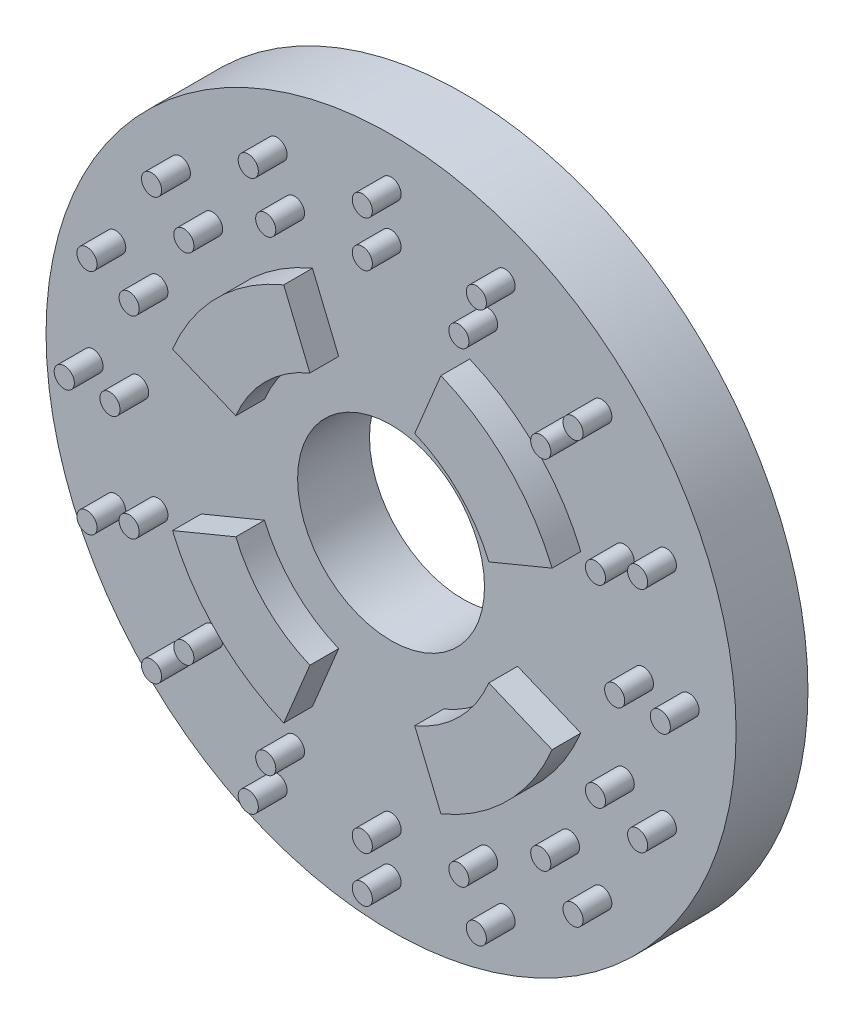
SolidWorks part; units mm, degrees
ref_plane "Front" through (0, 0, 0) normal (0, 0, 1) x (1, 0, 0)
ref_plane "Top" through (0, 0, 0) normal (0, 1, 0) x (1, 0, 0)
ref_plane "Right" through (0, 0, 0) normal (1, 0, 0) x (0, 0, -1)
sketch "Sketch1" plane through (0, 0, 0) normal (0, 0, 1) x (1, 0, 0)
  circle A0 centre (0, 0) radius 24
extrude "Extrude1" add sketch "Sketch1" along normal blind 5
sketch "Sketch4" plane through (0, 0, 5) normal (0, 0, 1) x (1, 0, 0)
  line L4 (0, 0) -> (7.933, -19.152) construction
  line L5 (0, 0) -> (19.152, -7.933) construction
  line L6 (0, 0) -> (19.152, 7.933) construction
  line L7 (0, 0) -> (7.933, 19.152) construction
  line L8 (0, 0) -> (-7.933, 19.152) construction
  line L9 (0, 0) -> (-19.152, 7.933) construction
  line L10 (0, 0) -> (-7.933, -19.152) construction
  line L11 (0, 0) -> (-19.152, -7.933) construction
  line L12 (3.6451, -8.8) -> (5.4676, -13.1999)
  line L13 (8.8, -3.6451) -> (13.1999, -5.4676)
  line L14 (8.8, 3.6451) -> (13.1999, 5.4676)
  line L15 (3.6451, 8.8) -> (5.4676, 13.1999)
  line L16 (-3.6451, 8.8) -> (-5.4676, 13.1999)
  line L17 (-8.8, 3.6451) -> (-13.1999, 5.4676)
  line L18 (-8.8, -3.6451) -> (-13.1999, -5.4676)
  line L19 (-5.4676, -13.1999) -> (-3.6451, -8.8)
  circle A0 centre (0, 20.73) radius 0.7
  circle A1 centre (0, -20.73) radius 0.7
  circle A2 centre (20.73, 0) radius 0.7
  circle A3 centre (-20.73, 0) radius 0.7
  circle A4 centre (-14.658, 14.658) radius 0.7
  circle A5 centre (14.658, 14.658) radius 0.7
  circle A6 centre (14.658, -14.658) radius 0.7
  circle A7 centre (-14.658, -14.658) radius 0.7
  circle A8 centre (19.152, 7.933) radius 0.7
  circle A9 centre (7.933, 19.152) radius 0.7
  circle A10 centre (19.152, -7.933) radius 0.7
  circle A11 centre (7.933, -19.152) radius 0.7
  circle A12 centre (-7.933, 19.152) radius 0.7
  circle A13 centre (-19.152, 7.933) radius 0.7
  circle A14 centre (-19.152, -7.933) radius 0.7
  circle A15 centre (-7.933, -19.152) radius 0.7
  arc A16 (5.4676, -13.1999) -> (13.1999, -5.4676) centre (0, 0) ccw
  arc A18 (3.6451, -8.8) -> (8.8, -3.6451) centre (0, 0) ccw
  arc A20 (8.8, 3.6451) -> (3.6451, 8.8) centre (0, 0) ccw
  arc A21 (13.1999, 5.4676) -> (5.4676, 13.1999) centre (0, 0) ccw
  arc A22 (-3.6451, 8.8) -> (-8.8, 3.6451) centre (0, 0) ccw
  arc A23 (-5.4676, 13.1999) -> (-13.1999, 5.4676) centre (0, 0) ccw
  arc A24 (-8.8, -3.6451) -> (-3.6451, -8.8) centre (0, 0) ccw
  arc A25 (-13.1999, -5.4676) -> (-5.4676, -13.1999) centre (0, 0) ccw
  circle A32 centre (0, 17.555) radius 0.7
  circle A33 centre (17.555, 0) radius 0.7
  circle A34 centre (0, -17.555) radius 0.7
  circle A35 centre (-17.555, 0) radius 0.7
  circle A36 centre (-12.413, 12.413) radius 0.7
  circle A37 centre (12.413, 12.413) radius 0.7
  circle A38 centre (12.413, -12.413) radius 0.7
  circle A39 centre (-12.413, -12.413) radius 0.7
  circle A40 centre (-16.218, 6.718) radius 0.7
  circle A41 centre (16.218, 6.718) radius 0.7
  circle A42 centre (16.218, -6.718) radius 0.7
  circle A43 centre (-16.218, -6.718) radius 0.7
  circle A44 centre (6.718, 16.218) radius 0.7
  circle A45 centre (6.718, -16.218) radius 0.7
  circle A46 centre (-6.718, -16.218) radius 0.7
  circle A47 centre (-6.718, 16.218) radius 0.7
sketch "Sketch5" plane through (0, 0, 0) normal (0, 0, -1) x (-1, 0, 0)
  circle A0 centre (0, 0) radius 6.5
extrude "Cut-Extrude3" cut sketch "Sketch5" against normal blind 10
extrude "Extrude2" add sketch "Sketch4" along normal blind 2
